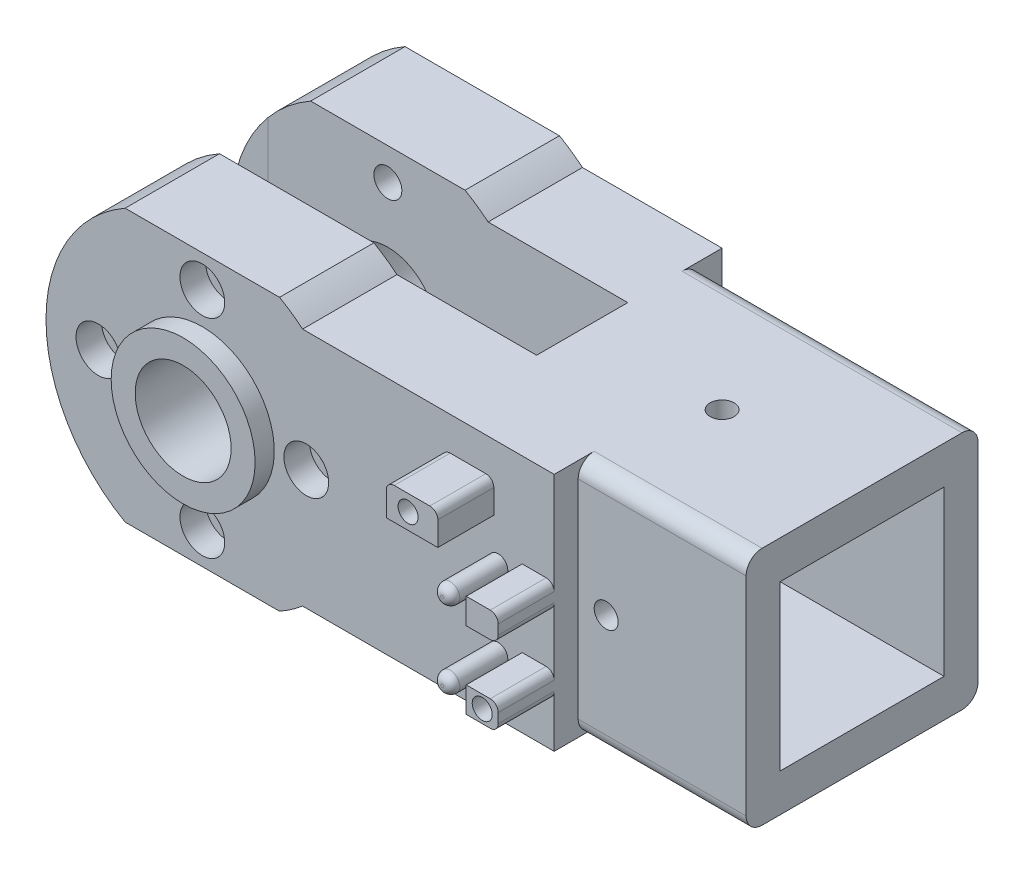
SolidWorks part; units mm, degrees
ref_plane "Piano frontale" through (0, 0, 0) normal (0, 0, 1) x (1, 0, 0)
ref_plane "Piano superiore" through (0, 0, 0) normal (0, 1, 0) x (1, 0, 0)
ref_plane "Piano destro" through (0, 0, 0) normal (1, 0, 0) x (0, 0, -1)
sketch "Schizzo11" plane through (0, 0, 0) normal (0, 0, 1) x (1, 0, 0)
  line L0 (-14.5, 15) -> (14.5, -15) construction
  line L1 (-14.5, 15) -> (14.5, 15)
  line L3 (-14.5, -15) -> (14.5, -15)
  line L4 (14.5, 15) -> (14.5, -15)
  line L5 (-14.5, -15) -> (-20.5, -15)
  line L6 (-20.5, -15) -> (-20.5, 15)
  line L7 (-20.5, 15) -> (-14.5, 15)
  line L8 (0, 15) -> (0, 0)
  line L9 (0, 0) -> (14.5, 0)
  point P5 (0, -15)
  dimension "D1" = 30
  dimension "D2" = 29
  dimension "D3" = 35
extrude "Estrusione-Estrusione4" add sketch "Schizzo11" along normal blind 29 contours L0 L7 L6 L5 L3 | L1 L0 L8 | L8 L9 L4 L1 | L9 L0 L4
sketch "Schizzo12" plane through (14.5, 0, 0) normal (1, 0, 0) x (0, 0, -1)
  line L1 (-4.25, -10.25) -> (-24.75, -10.25)
  line L2 (-4.25, -10.25) -> (-4.25, 10.25)
  line L3 (-4.25, 10.25) -> (-24.75, 10.25)
  line L4 (-24.75, -10.25) -> (-24.75, 10.25)
  line L5 (-4.25, -10.25) -> (-24.75, 10.25) construction
  line L6 (-4.25, 10.25) -> (-24.75, -10.25) construction
  line L8 (-29, 15) -> (0, -15) construction
  point P0 (-14.5, 0)
  point P8 (-14.5, 0)
  dimension "D2" = 20.5
  dimension "D3" = 20.5
extrude "Taglio-Estrusione5" cut sketch "Schizzo12" against normal blind 31
sketch "Schizzo13" plane through (0, -15, 0) normal (0, -1, 0) x (1, 0, 0)
  line L1 (14.5, 29) -> (-20.5, 29) construction
  line L2 (14.5, 29) -> (14.5, 0) construction
  circle A0 centre (-3, 14.5) radius 1.5
  point P7 (-3, 29)
  point P9 (14.5, 14.5)
  dimension "D2" = 3
extrude "Taglio-Estrusione6" cut sketch "Schizzo13" against normal through all
sketch "Schizzo14" plane through (0, 0, 29) normal (0, 0, 1) x (1, 0, 0)
  line L0 (-20.5, 15) -> (14.5, 15) construction
  line L1 (14.5, 15) -> (14.5, -15) construction
  circle A0 centre (-3, 0) radius 1.5
  point P6 (-3, 15)
  point P9 (14.5, 0)
  dimension "D1" = 3
extrude "Taglio-Estrusione7" cut sketch "Schizzo14" against normal blind 20
fillet "Raccordo6" radius 2 4 edges at (-3, -15, 0) (-3, -15, 29) (-3, 15, 0) (-3, 15, 29)
sketch "Schizzo15" plane through (-20.5, 0, 0) normal (-1, 0, 0) x (0, 0, 1)
  line L0 (27, 15) -> (2, 15) construction
  line L1 (20.2, 15) -> (32, 15)
  line L2 (20.2, 15) -> (20.2, -15)
  line L3 (20.2, -15) -> (32, -15)
  line L4 (32, 15) -> (32, -15)
  line L5 (27, -15) -> (2, -15) construction
  line L6 (8.8, 15) -> (20.2, 15) construction
  line L7 (-3, 15) -> (8.8, 15)
  line L8 (-3, 15) -> (-3, -15)
  line L9 (-3, -15) -> (8.8, -15)
  line L10 (8.8, 15) -> (8.8, -15)
  point P8 (14.5, 15)
  point P13 (14.5, 15)
  dimension "D1" = 11.8
  dimension "D2" = 11.4
  dimension "D3" = 11.8
extrude "Estrusione-Estrusione5" add sketch "Schizzo15" along normal blind 45
sketch "Schizzo16" plane through (0, 0, 32) normal (0, 0, 1) x (1, 0, 0)
  line L0 (-65.5, -15) -> (-65.5, 15) construction
  circle A0 centre (-50.5, 0) radius 6
  point P8 (-65.5, 0)
  dimension "D1" = 12
  dimension "D2" = 15
extrude "Taglio-Estrusione8" cut sketch "Schizzo16" against normal through all both and the other way through all
ref_plane "Piano1" through (0, 0, 14.5) normal (0, 0, 1) x (1, 0, 0)
sketch "Schizzo20" plane through (0, 0, -3) normal (0, 0, -1) x (-1, 0, 0)
  line L0 (65.5, 15) -> (20.5, 15) construction
  line L1 (37.962, 15) -> (65.5, 15)
  line L2 (37.962, 15) -> (37.962, -15)
  line L3 (37.962, -15) -> (65.5, -15)
  line L4 (65.5, 15) -> (65.5, -15)
  circle A0 centre (50.5, 0) radius 19.55
  dimension "D1" = 39.1
extrude "Estrusione-Estrusione7" add sketch "Schizzo20" against normal up to surface (11.8 mm away) separate body contours L4 A0 up to face at (-50.5, 6, 8.8)
sketch "Schizzo21" plane through (0, 0, 32) normal (0, 0, 1) x (1, 0, 0)
  line L0 (-65.5, -15) -> (-20.5, -15) construction
  line L1 (-65.5, 15) -> (-37.962, 15)
  line L2 (-65.5, 15) -> (-65.5, -15)
  line L3 (-65.5, -15) -> (-37.962, -15)
  line L4 (-37.962, 15) -> (-37.962, -15)
  circle A0 centre (-50.5, 0) radius 19.55
  arc A1 (-65.5, 12.538) -> (-65.5, -12.538) centre (-50.5, 0) ccw construction
extrude "Estrusione-Estrusione8" add sketch "Schizzo21" against normal up to surface (11.8 mm away) contours L2 A0 up to face at (-50.5, -6, 20.2)
sketch "Schizzo22" plane through (0, 0, 32) normal (0, 0, 1) x (1, 0, 0)
  line L0 (-65.5, -15) -> (-20.5, -15) construction
  line L1 (-65.5, 15) -> (-37.962, 15)
  line L2 (-65.5, 15) -> (-65.5, -15)
  line L3 (-65.5, -15) -> (-37.962, -15)
  line L4 (-37.962, 15) -> (-37.962, -15)
  circle A0 centre (-50.5, 0) radius 19.55
  arc A1 (-65.5, 12.538) -> (-65.5, -12.538) centre (-50.5, 0) ccw construction
  line M9 (-65.5, 15) -> (-65.5, 12.538)
  line M11 (-65.5, -12.538) -> (-65.5, -15)
  line M12 (-65.5, -15) -> (-20.5, -15)
extrude "Taglio-Estrusione10" cut sketch "Schizzo22" against normal through all both and the other way through all contours A0 M11 M12 | A0 L1 M9
sketch "Schizzo27" plane through (0, 0, 32) normal (0, 0, 1) x (1, 0, 0)
  line L0 (-20.5, -15) -> (-20.5, 15) construction
  line L1 (-20.5, 17) -> (-70.05, 17)
  line L2 (-20.5, 17) -> (-20.5, -17)
  line L3 (-20.5, -17) -> (-70.05, -17)
  line L4 (-70.05, 17) -> (-70.05, -17)
  line L5 (-63.038, 15) -> (-20.5, 15) construction
  line L6 (-63.038, -15) -> (-20.5, -15) construction
  circle A0 centre (-50.5, 0) radius 19.55
  line M9 (-63.038, -15) -> (-20.5, -15)
  line M15 (-20.5, 15) -> (-63.038, 15)
  dimension "D1" = 2
  dimension "D2" = 2
extrude "Estrusione-Estrusione9" add sketch "Schizzo27" against normal up to surface (11.8 mm away) contours A0 L1 M15 | A0 L3 M9 up to face at (-50.5, -6, 20.2)
sketch "Schizzo29" plane through (0, 0, -3) normal (0, 0, -1) x (-1, 0, 0)
  line L0 (40.8459, 17) -> (60.1541, 17)
  line L1 (60.1541, 17) -> (40.8459, 17) construction
  line L2 (40.8459, -17) -> (60.1541, -17)
  line L3 (63.038, -15) -> (37.962, -15)
  line L4 (37.962, 15) -> (63.038, 15)
  circle A0 centre (50.5, 0) radius 19.55
  arc A1 (65.5, 12.538) -> (63.038, 15) centre (50.5, 0) ccw construction
  line M7 (63.038, 15) -> (20.5, 15)
  line M9 (20.5, -15) -> (63.038, -15)
extrude "Estrusione-Estrusione10" add sketch "Schizzo29" against normal up to surface (11.8 mm away) contours L0 A0 M7 | A0 L2 M9 up to face at (-50.5, 6, 8.8)
sketch "Schizzo23" plane through (0, 0, 32) normal (0, 0, 1) x (1, 0, 0)
  circle A0 centre (-50.5, 0) radius 13 construction
  circle A1 centre (-63.5, 0) radius 1.75
  circle A3 centre (-50.5, 13) radius 1.75
  circle A4 centre (-50.5, -13) radius 1.75
  circle A5 centre (-37.5, 0) radius 1.75
  dimension "D1" = 26
  dimension "D2" = 3.5
extrude "Taglio-Estrusione11" cut sketch "Schizzo23" against normal through all both and the other way through all
sketch "Schizzo24" plane through (0, 0, 32) normal (0, 0, 1) x (1, 0, 0)
  circle A0 centre (-63.5, 0) radius 2.8
  circle A2 centre (-50.5, 13) radius 2.8
  circle A3 centre (-37.5, 0) radius 2.8
  circle A4 centre (-50.5, -13) radius 2.8
  dimension "D1" = 5.6
extrude "Taglio-Estrusione12" cut sketch "Schizzo24" against normal blind 3.2
sketch "Schizzo25" plane through (0, 0, -3) normal (0, 0, -1) x (-1, 0, 0)
  line L1 (63.5, 3.2332) -> (60.7, 1.6166)
  line L2 (60.7, 1.6166) -> (60.7, -1.6166)
  line L3 (60.7, -1.6166) -> (63.5, -3.2332)
  line L4 (63.5, -3.2332) -> (66.3, -1.6166)
  line L5 (66.3, -1.6166) -> (66.3, 1.6166)
  line L6 (66.3, 1.6166) -> (63.5, 3.2332)
  line L7 (50.5, 9.7668) -> (53.3, 11.3834)
  line L8 (53.3, 11.3834) -> (53.3, 14.6166)
  line L9 (53.3, 14.6166) -> (50.5, 16.2332)
  line L10 (50.5, 16.2332) -> (47.7, 14.6166)
  line L11 (47.7, 14.6166) -> (47.7, 11.3834)
  line L12 (47.7, 11.3834) -> (50.5, 9.7668)
  line L13 (37.5, -3.2332) -> (40.3, -1.6166)
  line L14 (40.3, -1.6166) -> (40.3, 1.6166)
  line L15 (40.3, 1.6166) -> (37.5, 3.2332)
  line L16 (37.5, 3.2332) -> (34.7, 1.6166)
  line L17 (34.7, 1.6166) -> (34.7, -1.6166)
  line L18 (34.7, -1.6166) -> (37.5, -3.2332)
  line L19 (50.5, -9.7668) -> (47.7, -11.3834)
  line L20 (47.7, -11.3834) -> (47.7, -14.6166)
  line L21 (47.7, -14.6166) -> (50.5, -16.2332)
  line L22 (50.5, -16.2332) -> (53.3, -14.6166)
  line L23 (53.3, -14.6166) -> (53.3, -11.3834)
  line L24 (53.3, -11.3834) -> (50.5, -9.7668)
  circle A0 centre (63.5, 0) radius 2.8 construction
  circle A1 centre (50.5, 13) radius 2.8 construction
  circle A2 centre (37.5, 0) radius 2.8 construction
  circle A3 centre (50.5, -13) radius 2.8 construction
  dimension "D1" = 5.6
extrude "Taglio-Estrusione13" cut sketch "Schizzo25" against normal blind 2.53
sketch "Schizzo31" plane through (0, 0, 32) normal (0, 0, 1) x (1, 0, 0)
  circle A0 centre (-50.5, 0) radius 9
  circle A1 centre (-50.5, 0) radius 6
  circle A2 centre (-50.5, 0) radius 6 construction
  dimension "D1" = 18
extrude "Estrusione-Estrusione16" add sketch "Schizzo31" along normal blind 2.4
mirror "Specchia3" about plane through (0, 0, 14.5) normal (0, 0, 1) of "Estrusione-Estrusione16"
sketch "Schizzo17" plane through (0, 0, 29) normal (0, 0, 1) x (1, 0, 0)
  line L0 (14.5, 13) -> (-20.5, 13) construction
  line L2 (-20.5, -15) -> (-20.5, 15) construction
  line L3 (-10.5, -9.5) -> (-6.5, -9.5)
  line L4 (-10.5, -9.5) -> (-10.5, -6.3)
  line L5 (-10.5, -6.3) -> (-6.5, -6.3)
  line L6 (-6.5, -9.5) -> (-6.5, -6.3)
  line L7 (-10.5, 0.1) -> (-6.5, 0.1)
  line L8 (-10.5, 0.1) -> (-10.5, 3.3)
  line L9 (-10.5, 3.3) -> (-6.5, 3.3)
  line L10 (-6.5, 0.1) -> (-6.5, 3.3)
  line L12 (-20.5, 10.8) -> (-20.5, 6.8)
  line L13 (-20.5, 6.8) -> (-14.049, 6.8)
  line L14 (-14.049, 10.8) -> (-14.049, 6.8)
  line L15 (-20.5, -13) -> (14.5, -13) construction
  line L16 (-20.5, -13) -> (-20.5, 13) construction
  line L17 (-20.5, 10.8) -> (-14.049, 10.8)
  line L18 (-20.5, 13) -> (-20.5, 15) construction
  circle A0 centre (-13.5, 1.7) radius 1.2
  circle A1 centre (-13.5, -7.9) radius 1.2
  dimension "D4" = 2.4
  dimension "D2" = 9.6
  dimension "D3" = 7
  dimension "D5" = 10
  dimension "D6" = 3.5
  dimension "D7" = 3.2
  dimension "D8" = 6.4
  dimension "D9" = 3.2
  dimension "D10" = 4
  dimension "D11" = 2.2
  dimension "D12" = 6.451
  dimension "D13" = 4
  dimension "D14" = 5.1
extrude "Estrusione-Estrusione6" add sketch "Schizzo17" along normal blind 10
fillet "Raccordo9" radius 1 8 edges at (-6.5, -9.5, 34) (-6.5, -6.3, 34) (-6.5, 0.1, 34) (-6.5, 3.3, 34) (-12.3, 1.7, 39) (-12.3, -7.9, 39) (-14.049, 10.8, 34) (-20.5, 10.8, 35.5)
sketch "Schizzo19" plane through (0, 0, 39) normal (0, 0, 1) x (1, 0, 0)
  line L1 (-10.5, 3.3) -> (-10.5, 0.1) construction
  line L2 (-15.049, 10.8) -> (-19.5, 10.8) construction
  line L3 (-15.049, 10.8) -> (-20.5, 10.8) construction
  line L4 (-10.5, -6.3) -> (-10.5, -9.5) construction
  circle A0 centre (-8.5, -7.9) radius 1.25
  circle A2 centre (-17.7745, 8.8) radius 1.25
  point P6 (-10.5, -7.9)
  point P16 (-17.7745, 10.8)
  dimension "D3" = 2.5
  dimension "D4" = 2.5
  dimension "D1" = 2
  dimension "D2" = 2
extrude "Taglio-Estrusione9" cut sketch "Schizzo19" against normal blind 8
sketch "Schizzo33" plane through (0, 0, 29) normal (0, 0, 1) x (1, 0, 0)
  line L0 (-6.5, 1.1) -> (-6.5, 2.3) construction
  line L1 (-20.5, -15) -> (-6.5, -15)
  line L2 (-20.5, -15) -> (-20.5, 15)
  line L3 (-20.5, 15) -> (-6.5, 15)
  line L4 (-6.5, -15) -> (-6.5, 15)
  line L5 (14.5, -15) -> (-20.5, -15) construction
  line L6 (-20.5, 15) -> (14.5, 15) construction
  line L7 (-20.5, -15) -> (-20.5, 6.8) construction
extrude "Estrusione-Estrusione17" add sketch "Schizzo33" along normal blind 3 and the other way up to next
